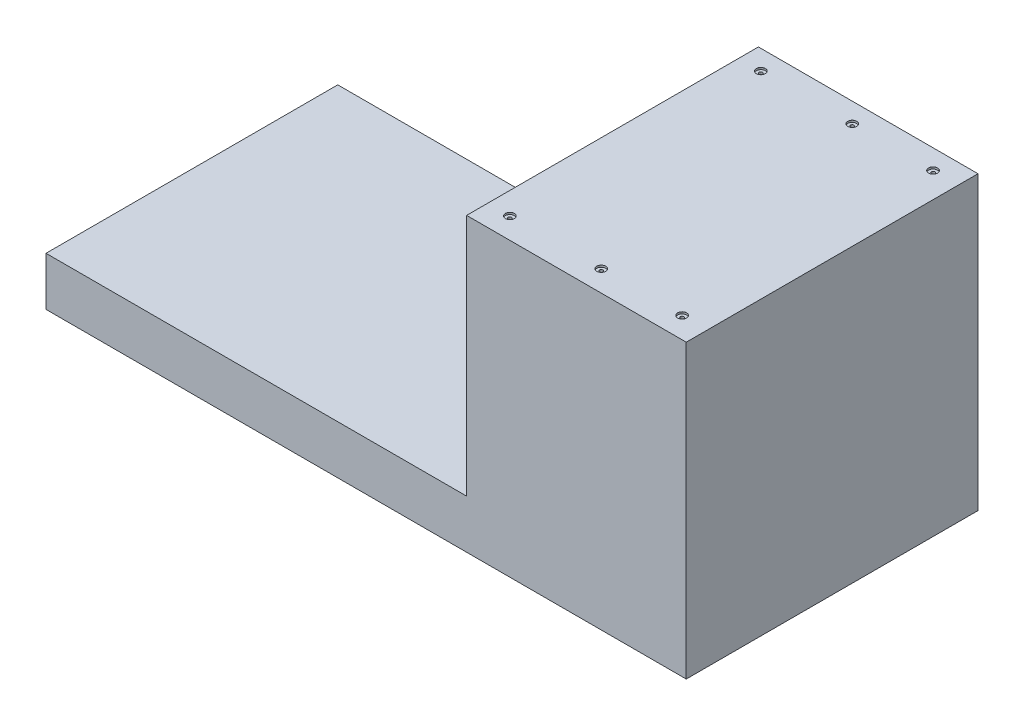
SolidWorks part; units mm, degrees
ref_plane "Front Plane" through (0, 0, 0) normal (0, 0, 1) x (1, 0, 0)
ref_plane "Top Plane" through (0, 0, 0) normal (0, 1, 0) x (1, 0, 0)
ref_plane "Right Plane" through (0, 0, 0) normal (1, 0, 0) x (0, 0, -1)
sketch "Sketch1" plane through (0, 0, 0) normal (0, 1, 0) x (1, 0, 0)
  line L1 (-254, 152.4) -> (254, 152.4)
  line L2 (-254, 152.4) -> (-254, -152.4)
  line L3 (-254, -152.4) -> (254, -152.4)
  line L4 (254, 152.4) -> (254, -152.4)
  line L5 (-254, 152.4) -> (254, -152.4) construction
  line L6 (-254, -152.4) -> (254, 152.4) construction
  point P0 (0, 0)
  dimension "D1" = 508
  dimension "D2" = 304.8
extrude "Boss-Extrude1" add sketch "Sketch1" along normal blind 50.8
sketch "Sketch2" plane through (0, 50.8, 0) normal (0, 1, 0) x (1, 0, 0)
  line L0 (254, 152.4) -> (254, -152.4)
  line L1 (254, -152.4) -> (24.5768, -152.4)
  line L2 (-254, -152.4) -> (254, -152.4) construction
  line L3 (24.5768, -152.4) -> (24.5768, 152.4)
  line L4 (254, 152.4) -> (-254, 152.4) construction
  line L5 (24.5768, 152.4) -> (254, 152.4)
extrude "Boss-Extrude2" add sketch "Sketch2" along normal blind 254
sketch "Sketch3" plane through (0, 0, 152.4) normal (0, 0, 1) x (1, 0, 0)
  line L0 (-254, 0) -> (-414.8516, 0)
  line L1 (-254, 50.8) -> (-414.8516, 50.8)
  line L2 (-414.8516, 50.8) -> (-414.8516, 0)
  line L9 (-254, 0) -> (254, 0)
  line L10 (254, 0) -> (254, 304.8)
  line L11 (254, 304.8) -> (24.5768, 304.8)
  line L12 (24.5768, 304.8) -> (24.5768, 50.8)
  line L13 (24.5768, 50.8) -> (-254, 50.8)
  line L14 (-254, 50.8) -> (-254, 0)
  line L15 (-254, 0) -> (254, 0)
  line L16 (254, 0) -> (254, 304.8)
  line L17 (254, 304.8) -> (24.5768, 304.8)
  line L18 (24.5768, 304.8) -> (24.5768, 50.8)
  line L19 (24.5768, 50.8) -> (-254, 50.8)
  dimension "D1" = 0
extrude "Boss-Extrude3" add sketch "Sketch3" against normal blind 304.8
hole_wizard "CBORE for M3 Hex Head Cap Screw1" positions "Sketch5" profile "Sketch6" counterbore size "M3" standard "ISO" end condition up to next
sketch "Sketch5" plane through (0, 304.8, 0) normal (0, 1, 0) x (1, 0, 0)
  point P0 (47.7194, 131.8169)
  point P2 (143.1857, 131.8169)
  point P4 (227.6366, 131.8169)
  point P6 (227.6366, -130.3482)
  point P8 (143.1857, -130.3482)
  point P10 (47.7194, -130.3482)
sketch "Sketch6" plane through (47.7194, 304.8, -131.8169) normal (1, 0, 0) x (0, 0, 1)
  line L0 (0, 0) -> (0, 304.8)
  line L1 (0, 304.8) -> (1.8, 304.8)
  line L3 (1.8, 304.8) -> (1.8, 2)
  line L4 (4.6755, 2) -> (1.8, 2)
  line L5 (4.6755, 2) -> (4.6755, 0.025)
  line L6 (4.6755, 0.025) -> (4.7005, 0)
  line L7 (4.7005, 0) -> (0, 0)
  line L8 (-4.6755, 0.025) -> (-4.7005, 0) construction
  line L11 (0, -6.35) -> (0, 107.95) construction
  dimension "Thru Hole Dia." = 3.6
  dimension "Thru Hole Depth" = 304.8
  dimension "C'Bore Dia." = 9.351
  dimension "C'Bore Depth" = 2
  dimension "Near C'Sink Dia." = 9.401
  dimension "Near C'Sink Angle" = 90
